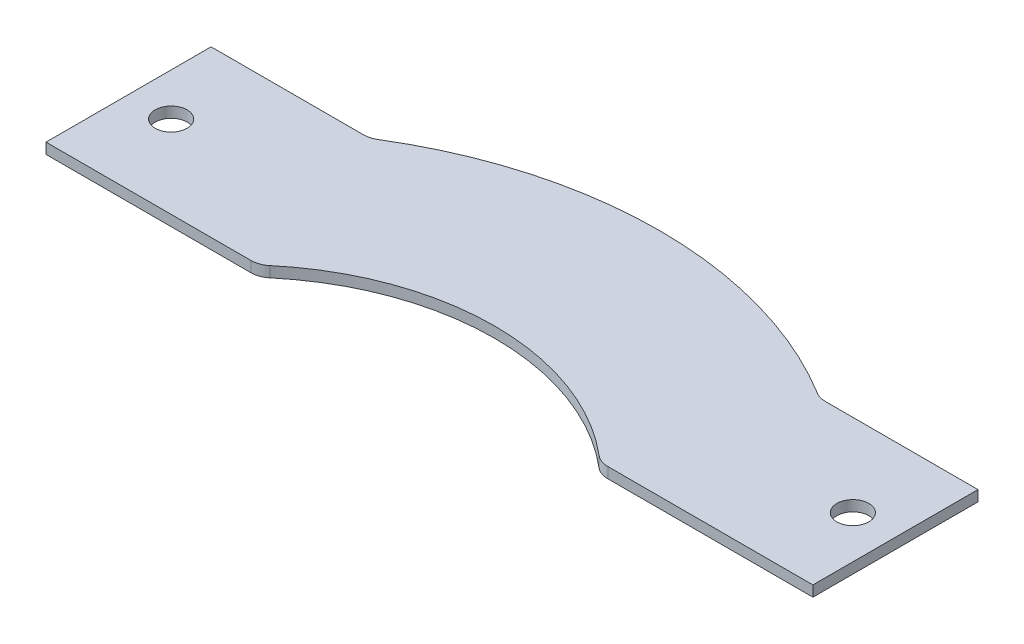
SolidWorks part; units mm, degrees
ref_plane "Front Plane" through (0, 0, 0) normal (0, 0, 1) x (1, 0, 0)
ref_plane "Top Plane" through (0, 0, 0) normal (0, 1, 0) x (1, 0, 0)
ref_plane "Right Plane" through (0, 0, 0) normal (1, 0, 0) x (0, 0, -1)
sketch "Sketch1" plane through (0, 0, 0) normal (0, 1, 0) x (1, 0, 0)
  line L0 (68.8251, 106.0086) -> (114.3, 106.0086)
  line L1 (114.3, 56.7961) -> (53.1702, 56.7961)
  line L2 (-53.1702, 56.7961) -> (-114.3, 56.7961)
  line L3 (-68.8251, 106.0086) -> (-114.3, 106.0086)
  line L4 (114.3, 56.7961) -> (114.3, 106.0086)
  line L5 (-114.3, 56.7961) -> (-114.3, 106.0086)
  line L6 (0, 0) -> (114.3, 0) construction
  line L7 (-114.3, 56.7961) -> (-114.3, 17.0712)
  arc A0 (-49.0802, 58.2887) -> (49.0802, 58.2887) centre (0, 0) cw
  arc A1 (-65.5082, 106.9438) -> (65.5082, 106.9438) centre (0, 0) cw
  arc A2 (53.1702, 56.7961) -> (49.0802, 58.2887) centre (53.1702, 63.1461) cw
  arc A3 (68.8251, 106.0086) -> (65.5082, 106.9438) centre (68.8251, 112.3586) cw
  arc A4 (-65.5082, 106.9438) -> (-68.8251, 106.0086) centre (-68.8251, 112.3586) cw
  arc A5 (-53.1702, 56.7961) -> (-49.0802, 58.2887) centre (-53.1702, 63.1461) ccw
  circle A6 centre (-101.6, 81.4024) radius 4.7625
  circle A7 centre (101.6, 81.4024) radius 4.7625
  point P12 (50.8, 56.7961)
  point P19 (-50.8, 56.7961)
  dimension "D1" = 76.2
  dimension "D2" = 49.2125
  dimension "D7" = 6.35
  dimension "D4" = 125.4125
  dimension "D10" = 9.525
  dimension "D11" = 9.525
  dimension "D3" = 49.2125
  dimension "D5" = 50.8
  dimension "D6" = 50.8
  dimension "D8" = 114.3
  dimension "D9" = 114.3
  dimension "D12" = 12.7
  dimension "D13" = 12.7
  dimension "D14" = 24.6062
  dimension "D15" = 24.6062
extrude "Extrude1" add sketch "Sketch1" along normal blind 3.175 contours L2 A5 A0 A2 L1 L4 L0 A3 A1 A4 L3 L5 A7 A6
